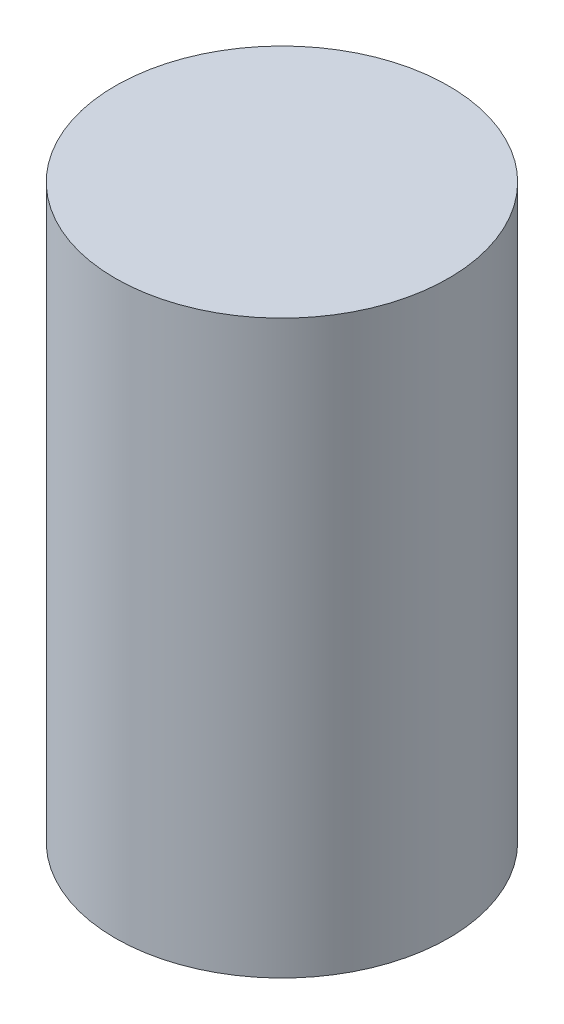
SolidWorks part; units mm, degrees
ref_plane "Front Plane" through (0, 0, 0) normal (0, 0, 1) x (1, 0, 0)
ref_plane "Top Plane" through (0, 0, 0) normal (0, 1, 0) x (1, 0, 0)
ref_plane "Right Plane" through (0, 0, 0) normal (1, 0, 0) x (0, 0, -1)
sketch "Sketch1" plane through (0, 0, 0) normal (0, 1, 0) x (1, 0, 0)
  circle A0 centre (0, 0) radius 44.45
  dimension "D1" = 88.9
extrude "Boss-Extrude1" add sketch "Sketch1" along normal mid plane 152.4
